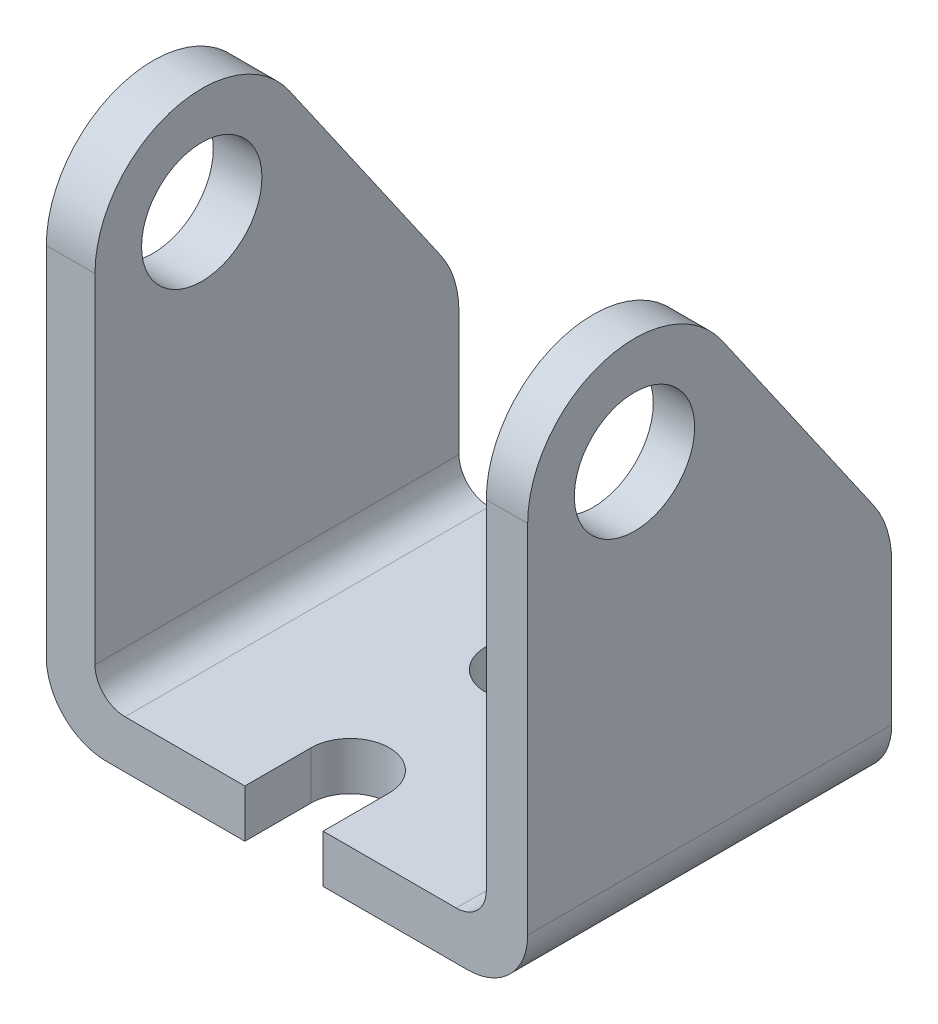
SolidWorks part; units mm, degrees
ref_plane "Front Plane" through (0, 0, 0) normal (0, 0, 1) x (1, 0, 0)
ref_plane "Top Plane" through (0, 0, 0) normal (0, 1, 0) x (1, 0, 0)
ref_plane "Right Plane" through (0, 0, 0) normal (1, 0, 0) x (0, 0, -1)
sketch "Sketch1" plane through (0, 0, 0) normal (0, 0, 1) x (1, 0, 0)
  line L0 (0, 0) -> (40.64, 0)
  line L1 (40.64, 0) -> (40.64, 44.196)
  line L2 (40.64, 44.196) -> (37.1473, 44.196)
  line L3 (0, 0) -> (0, 44.196)
  line L4 (37.1473, 44.196) -> (37.1473, 4.0432)
  line L5 (0, 44.196) -> (4.1072, 44.196)
  line L6 (4.1072, 44.196) -> (4.1072, 4.0432)
  line L7 (4.1072, 4.0432) -> (37.1473, 4.0432)
  dimension "D1" = 44.196
  dimension "D2" = 40.64
extrude "Boss-Extrude1" add sketch "Sketch1" along normal blind 30.734
sketch "Sketch2" plane through (0, 0, 0) normal (0, -1, 0) x (1, 0, 0)
  line L0 (40.64, 30.734) -> (40.64, 0) construction
  line L1 (16.764, 30.734) -> (23.368, 30.734)
  line L4 (37.1473, 30.734) -> (4.1072, 30.734) construction
  line L5 (40.64, 30.734) -> (40.64, 0) construction
  line L6 (0, 0) -> (40.64, 0) construction
  line L7 (23.368, 30.734) -> (23.368, 25.146)
  line L8 (16.764, 25.146) -> (16.764, 30.734)
  line L9 (37.1473, 0) -> (4.1072, 0) construction
  line L10 (31.1936, 21.844) -> (12.1383, 21.844) construction
  circle A2 centre (20.066, 10.414) radius 3.302
  arc A3 (23.368, 25.146) -> (16.764, 25.146) centre (20.066, 25.146) cw
  point P1 (20.066, 21.844)
  dimension "D1" = 3.302
  dimension "D2" = 5.588
  dimension "D4" = 6.604
  dimension "D3" = 20.574
  dimension "D5" = 10.414
  dimension "D6" = 20.574
extrude "Cut-Extrude3" cut sketch "Sketch2" against normal through all
fillet "Fillet3" radius 5.08 2 edges at (40.64, 0, 15.367) (0, 0, 15.367)
fillet "Fillet4" radius 2.54 2 edges at (37.1473, 4.0432, 15.367) (4.1072, 4.0432, 15.367)
sketch "Sketch3" plane through (0, 0, 0) normal (1, 0, 0) x (0, 0, -1)
  line L0 (-30.734, 5.08) -> (-30.734, 44.196) construction
  line L5 (-30.734, 44.196) -> (0, 44.196) construction
  circle A0 centre (-21.717, 35.179) radius 5.08
  dimension "D1" = 9.017
  dimension "D2" = 9.017
  dimension "D3" = 10.16
extrude "Cut-Extrude5" cut sketch "Sketch3" against normal through all and the other way through all
sketch "Sketch6" plane through (0, 0, 0) normal (1, 0, 0) x (0, 0, -1)
  line L1 (-30.734, 35.179) -> (-30.734, 44.196)
  line L2 (-30.734, 44.196) -> (0, 44.196)
  line L3 (-14.308, 40.3184) -> (-1.524, 21.8889)
  line L4 (0, 5.08) -> (0, 44.196) construction
  line L6 (0, 0) -> (-30.734, 0)
  line L7 (-30.734, 0) -> (-30.734, 5.08)
  line L8 (0, 44.196) -> (0, 17.018)
  line L10 (-30.734, 5.08) -> (-30.734, 44.196) construction
  line L11 (-30.734, 44.196) -> (0, 44.196) construction
  line L12 (-30.734, 0) -> (-44.8109, 0)
  arc A0 (-30.734, 35.179) -> (-21.717, 44.196) centre (-21.717, 35.179) cw
  arc A1 (-21.717, 44.196) -> (-14.308, 40.3184) centre (-21.717, 35.179) cw
  arc A2 (-1.524, 21.8889) -> (0, 17.018) centre (-8.5459, 17.018) cw
  circle A4 centre (-21.717, 35.179) radius 5.08 construction
  dimension "D1" = 17.018
  dimension "D2" = 29.21
extrude "Cut-Extrude14" cut sketch "Sketch6" against normal through all and the other way through all contours L1 A0 L2 | L3 A2 L8 L2 A1
